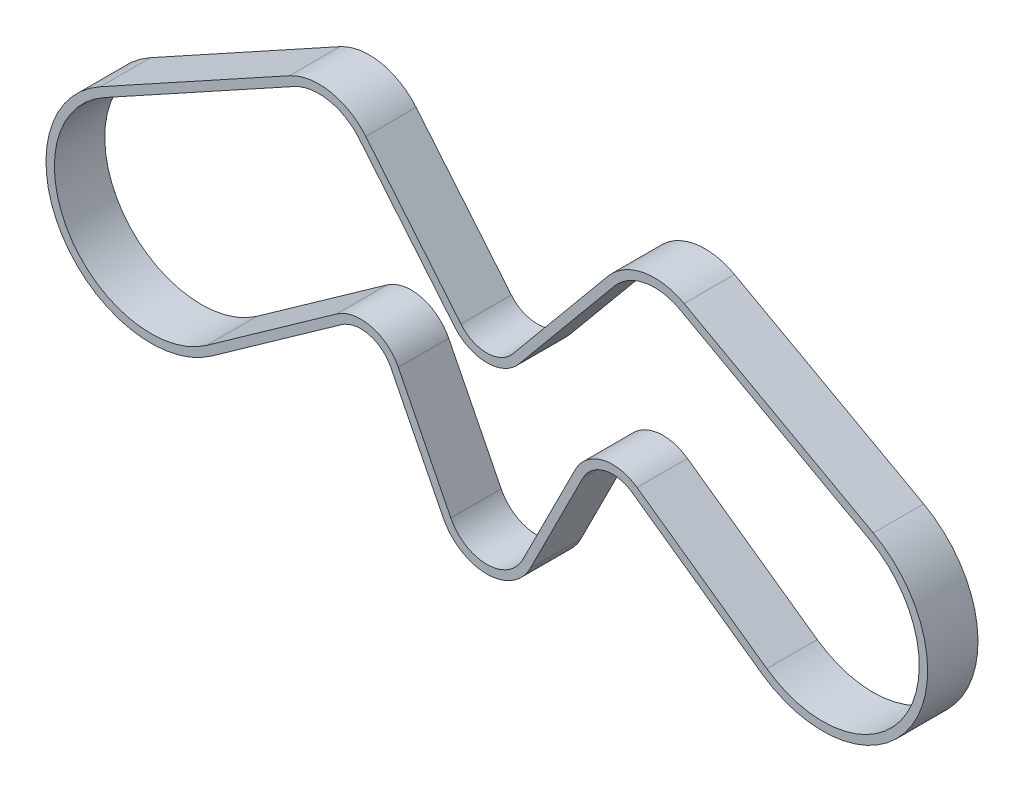
SolidWorks part; units mm, degrees
material "Caucho"
ref_plane "Alzado" through (0, 0, 0) normal (0, 0, 1) x (1, 0, 0)
ref_plane "Planta" through (0, 0, 0) normal (0, 1, 0) x (1, 0, 0)
ref_plane "Vista lateral" through (0, 0, 0) normal (1, 0, 0) x (0, 0, -1)
sketch "Croquis1" plane through (0, 0, 0) normal (0, 0, 1) x (1, 0, 0)
  line L0 (0, 0) -> (1, 0) construction
  line L1 (0, 0) -> (0, 1) construction
  line L2 (-5.5449, 10.0749) -> (16.9865, 22.4755)
  line L3 (24.8119, 20.9885) -> (36.1505, 7.3092)
  line L4 (43.8495, 7.3092) -> (55.1881, 20.9885)
  line L5 (63.0135, 22.4755) -> (85.5449, 10.0749)
  line L6 (73.3481, -9.3809) -> (57.8921, 1.5787)
  line L7 (50.5341, -0.2515) -> (44.2872, -12.6586)
  line L8 (35.7128, -12.6586) -> (29.4659, -0.2515)
  line L9 (22.1079, 1.5787) -> (6.6519, -9.3809)
  line L10 (-6.0271, 10.951) -> (16.5043, 23.3516)
  line L11 (25.5818, 21.6267) -> (36.9204, 7.9474)
  line L12 (43.0796, 7.9474) -> (54.4182, 21.6267)
  line L13 (63.4957, 23.3516) -> (86.0271, 10.951)
  line L14 (72.7697, -10.1967) -> (57.3137, 0.7629)
  line L15 (51.4273, -0.7012) -> (45.1804, -13.1083)
  line L16 (34.8196, -13.1083) -> (28.5727, -0.7012)
  line L17 (22.6863, 0.7629) -> (7.2303, -10.1967)
  line L18 (-1, -1) -> (-1, 1)
  line L19 (-1, -1) -> (1, -1)
  arc A0 (6.6519, -9.3809) -> (-5.5449, 10.0749) centre (0, 0) cw
  arc A1 (16.9865, 22.4755) -> (24.8119, 20.9885) centre (20, 17) cw
  arc A2 (36.1505, 7.3092) -> (43.8495, 7.3092) centre (40, 10.5) ccw
  arc A3 (55.1881, 20.9885) -> (63.0135, 22.4755) centre (60, 17) cw
  arc A4 (85.5449, 10.0749) -> (73.3481, -9.3809) centre (80, 0) cw
  arc A5 (57.8921, 1.5787) -> (50.5341, -0.2515) centre (55, -2.5) ccw
  arc A6 (44.2872, -12.6586) -> (35.7128, -12.6586) centre (40, -10.5) cw
  arc A7 (29.4659, -0.2515) -> (22.1079, 1.5787) centre (25, -2.5) ccw
  arc A8 (16.5043, 23.3516) -> (25.5818, 21.6267) centre (20, 17) cw
  arc A9 (36.9204, 7.9474) -> (43.0796, 7.9474) centre (40, 10.5) ccw
  arc A10 (54.4182, 21.6267) -> (63.4957, 23.3516) centre (60, 17) cw
  arc A11 (86.0271, 10.951) -> (72.7697, -10.1967) centre (80, 0) cw
  arc A12 (57.3137, 0.7629) -> (51.4273, -0.7012) centre (55, -2.5) ccw
  arc A13 (45.1804, -13.1083) -> (34.8196, -13.1083) centre (40, -10.5) cw
  arc A14 (28.5727, -0.7012) -> (22.6863, 0.7629) centre (25, -2.5) ccw
  arc A15 (7.2303, -10.1967) -> (-6.0271, 10.951) centre (0, 0) cw
  dimension "D1" = 1
extrude "Saliente-Extruir1" add sketch "Croquis1" along normal blind 6 contours A15 L17 A14 L16 A13 L15 A12 L14 A11 L13 A10 L12 A9 L11 A8 L10 L8 A7 L9 A0 L2 A1 L3 A2 L4 A3 L5 A4 L6 A5 L7 A6
